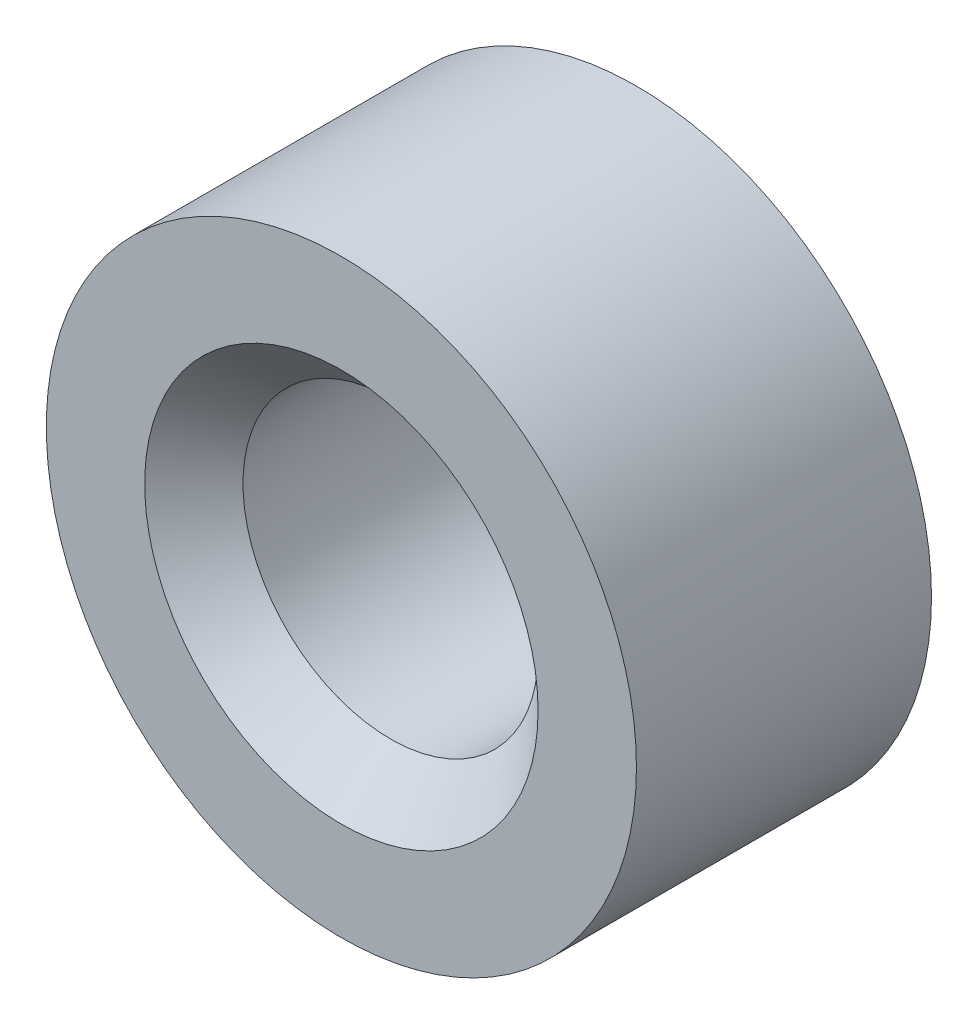
SolidWorks part; units mm, degrees
ref_plane "Piano frontale" through (0, 0, 0) normal (0, 0, 1) x (1, 0, 0)
ref_plane "Piano superiore" through (0, 0, 0) normal (0, 1, 0) x (1, 0, 0)
ref_plane "Piano destro" through (0, 0, 0) normal (1, 0, 0) x (0, 0, -1)
sketch "Schizzo1" plane through (0, 0, 0) normal (0, 0, 1) x (1, 0, 0)
  circle A0 centre (0, 0) radius 3
  circle A1 centre (0, 0) radius 1.5
  dimension "D1" = 3
  dimension "D2" = 6
extrude "Estrusione-Estrusione1" add sketch "Schizzo1" along normal blind 3
chamfer "Smusso1" distance 0.5 angle 45 1 edges at (1.5, 0, 3)
chamfer "Chamfer1" distance 0.5 angle 45 1 edges at (1.5, 0, 0)
